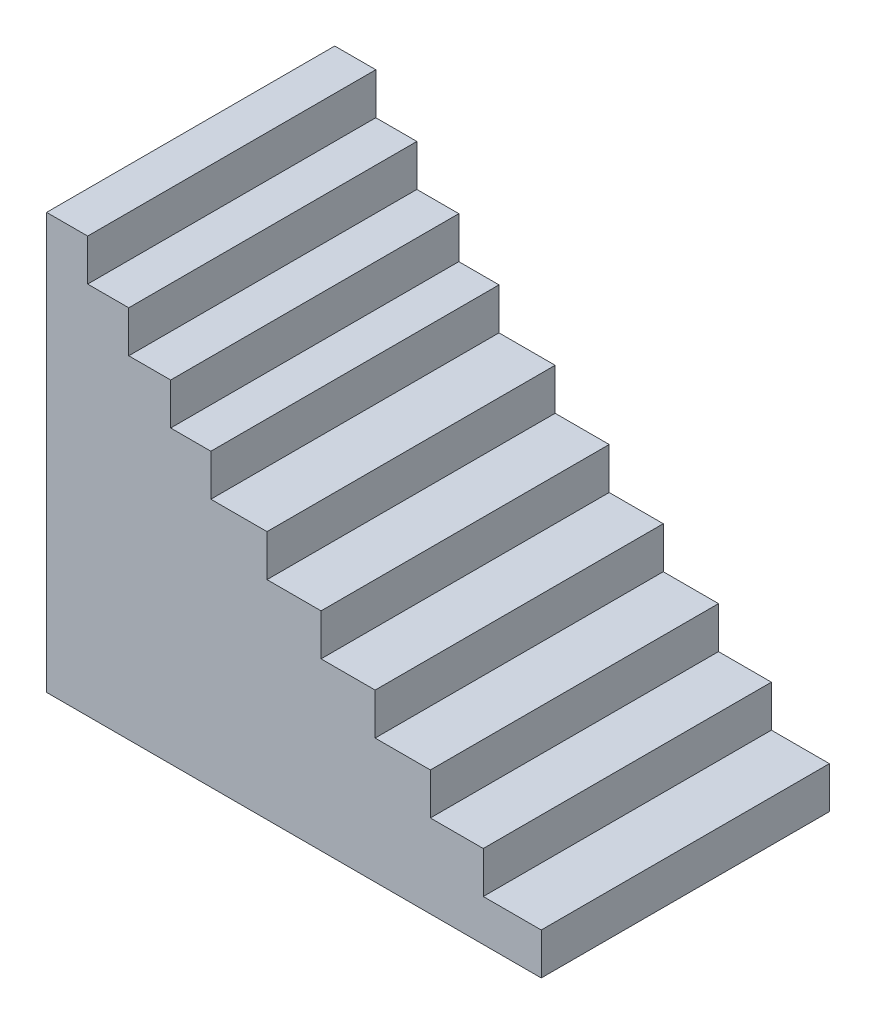
SolidWorks part; units mm, degrees
ref_plane "Alzado" through (0, 0, 0) normal (0, 0, 1) x (1, 0, 0)
ref_plane "Planta" through (0, 0, 0) normal (0, 1, 0) x (1, 0, 0)
ref_plane "Vista lateral" through (0, 0, 0) normal (1, 0, 0) x (0, 0, -1)
sketch "Croquis1" plane through (0, 0, 0) normal (0, 0, 1) x (1, 0, 0)
  line L1 (0, 0) -> (1200, 0)
  line L2 (0, 0) -> (0, 130)
  line L3 (0, 130) -> (1200, 130)
  line L4 (1200, 0) -> (1200, 130)
  line L5 (0, 130) -> (1027.2755, 130)
  line L6 (0, 130) -> (0, 260)
  line L7 (0, 260) -> (1027.2755, 260)
  line L8 (1027.2755, 130) -> (1027.2755, 260)
  line L9 (0, 260) -> (858.2195, 260)
  line L10 (0, 260) -> (0, 390)
  line L11 (0, 390) -> (858.2195, 390)
  line L12 (858.2195, 260) -> (858.2195, 390)
  line L13 (0, 390) -> (689.1636, 390)
  line L14 (0, 390) -> (0, 520)
  line L15 (0, 520) -> (689.1636, 520)
  line L16 (689.1636, 390) -> (689.1636, 520)
  line L17 (0, 520) -> (513.6377, 520)
  line L18 (0, 520) -> (0, 650)
  line L19 (0, 650) -> (513.6377, 650)
  line L20 (513.6377, 520) -> (513.6377, 650)
  line L21 (0, 650) -> (387.9366, 650)
  line L22 (0, 650) -> (0, 780)
  line L23 (0, 780) -> (387.9366, 780)
  line L24 (387.9366, 650) -> (387.9366, 780)
  line L25 (0, 780) -> (256.8189, 780)
  line L26 (0, 780) -> (0, 910)
  line L27 (0, 910) -> (256.8189, 910)
  line L28 (256.8189, 780) -> (256.8189, 910)
  line L29 (0, 910) -> (128.4094, 910)
  line L30 (0, 910) -> (0, 1040)
  line L31 (0, 1040) -> (128.4094, 1040)
  line L32 (128.4094, 910) -> (128.4094, 1040)
  line L33 (0, 0) -> (1365.3874, 0)
  line L34 (0, 0) -> (0, -130)
  line L35 (0, -130) -> (1365.3874, -130)
  line L36 (1365.3874, 0) -> (1365.3874, -130)
  line L37 (0, -130) -> (1546.7383, -130)
  line L38 (0, -130) -> (0, -260)
  line L39 (0, -260) -> (1546.7383, -260)
  line L40 (1546.7383, -130) -> (1546.7383, -260)
  dimension "D1" = 130
  dimension "D2" = 1200
  dimension "D3" = 130
  dimension "D4" = 130
  dimension "D5" = 130
  dimension "D6" = 130
  dimension "D7" = 130
  dimension "D8" = 130
  dimension "D9" = 130
  dimension "D10" = 130
  dimension "D11" = 130
extrude "Saliente-Extruir1" add sketch "Croquis1" along normal blind 901 contours L27 L32 L31 L30 | L23 L28 L27 L26 | L19 L24 L23 L22 | L15 L20 L19 L18 | L11 L16 L15 L14 | L7 L12 L11 L10 | L3 L8 L7 L6 | L1 L4 L3 L2 | L36 L33 L1 L34 L35 | L40 L37 L35 L38 L39
